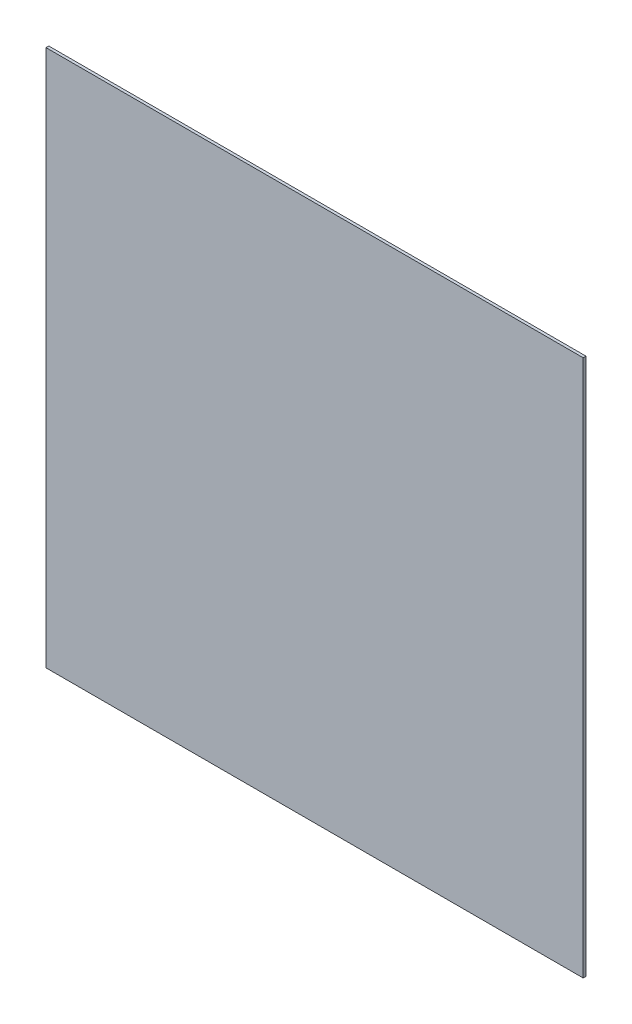
SolidWorks part; units mm, degrees
material "PC High Viscosity"
ref_plane "Front Plane" through (0, 0, 0) normal (0, 0, 1) x (1, 0, 0)
ref_plane "Top Plane" through (0, 0, 0) normal (0, 1, 0) x (1, 0, 0)
ref_plane "Right Plane" through (0, 0, 0) normal (1, 0, 0) x (0, 0, -1)
sketch "Sketch1" plane through (0, 0, 0) normal (0, 0, 1) x (1, 0, 0)
  line L1 (304.8, -304.8) -> (-304.8, -304.8)
  line L2 (304.8, -304.8) -> (304.8, 304.8)
  line L3 (304.8, 304.8) -> (-304.8, 304.8)
  line L4 (-304.8, -304.8) -> (-304.8, 304.8)
  line L5 (304.8, -304.8) -> (-304.8, 304.8) construction
  line L6 (304.8, 304.8) -> (-304.8, -304.8) construction
  point P0 (0, 0)
  dimension "D1" = 609.6
  dimension "D2" = 609.6
extrude "Boss-Extrude1" add sketch "Sketch1" along normal mid plane 3.175
hole_wizard "1 (1) Diameter Hole1" positions "Sketch2" profile "Sketch3" hole size "1" standard "ANSI Inch"
sketch "Sketch2" plane through (0, 0, 1.5875) normal (0, 0, 1) x (1, 0, 0)
  point P0 (0, 0)
sketch "Sketch3" plane through (0, 0, 1.5875) normal (1, 0, 0) x (0, -1, 0)
  line L0 (0, 0) -> (0, 3.175)
  line L1 (0, 3.175) -> (12.7, 3.175)
  line L2 (12.7, 3.175) -> (12.7, 0)
  line L5 (12.7, 0) -> (0, 0)
  line L11 (0, -6.35) -> (0, 107.95) construction
  dimension "Thru Hole Dia." = 25.4
  dimension "Thru Hole Depth" = 3.175
